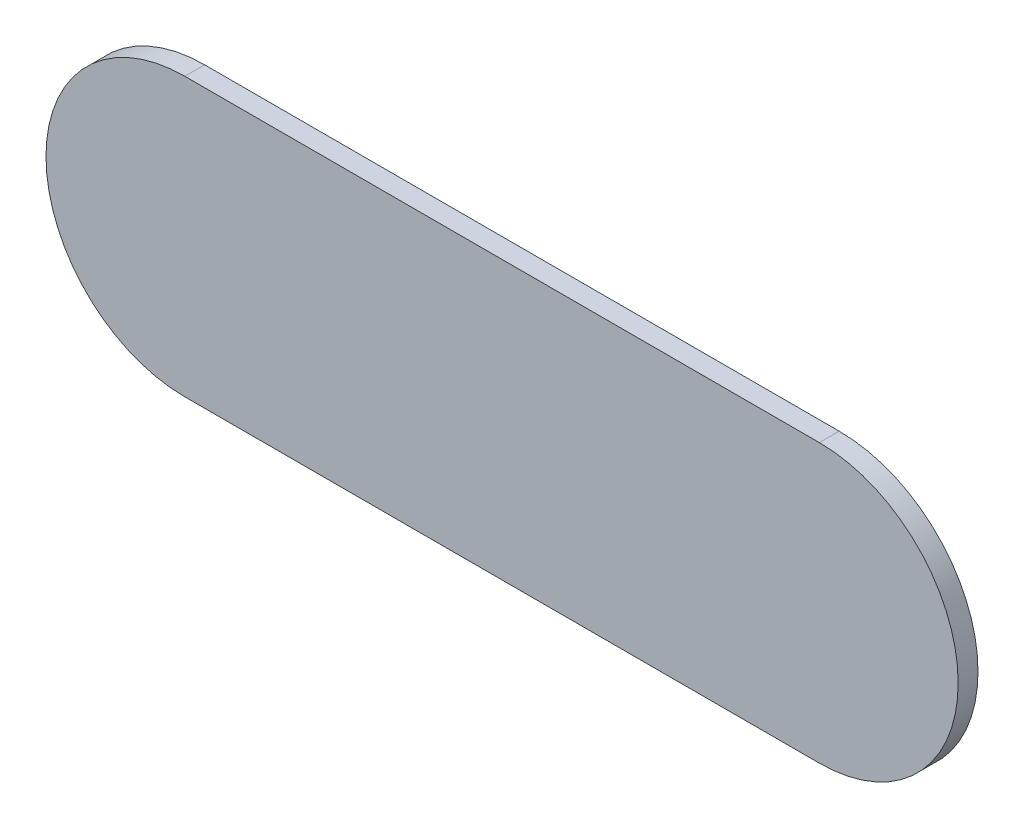
SolidWorks part; units mm, degrees
material "Plain Carbon Steel"
ref_plane "Front Plane" through (0, 0, 0) normal (0, 0, 1) x (1, 0, 0)
ref_plane "Top Plane" through (0, 0, 0) normal (0, 1, 0) x (1, 0, 0)
ref_plane "Right Plane" through (0, 0, 0) normal (1, 0, 0) x (0, 0, -1)
sketch "Sketch1" plane through (0, 0, 0) normal (0, 0, 1) x (1, 0, 0)
  line L0 (0, 0) -> (50.8, 0) construction
  line L1 (0, 11.1125) -> (50.8, 11.1125)
  line L2 (0, -11.1125) -> (50.8, -11.1125)
  arc A0 (0, 11.1125) -> (0, -11.1125) centre (0, 0) ccw
  arc A1 (50.8, -11.1125) -> (50.8, 11.1125) centre (50.8, 0) ccw
  point P3 (25.4, 0)
  dimension "D1" = 11.1125
  dimension "D2" = 50.8
extrude "Boss-Extrude1" add sketch "Sketch1" along normal blind 1.5875
sketch "Sketch2" plane through (0, 0, 0) normal (0, 0, -1) x (-1, 0, 0)
  line L0 (-11.1125, 11.1125) -> (-11.1125, -11.1125)
  line L1 (-50.8, 11.1125) -> (0, 11.1125) construction
  line L2 (0, -11.1125) -> (-50.8, -11.1125) construction
  dimension "D1" = 11.1125
